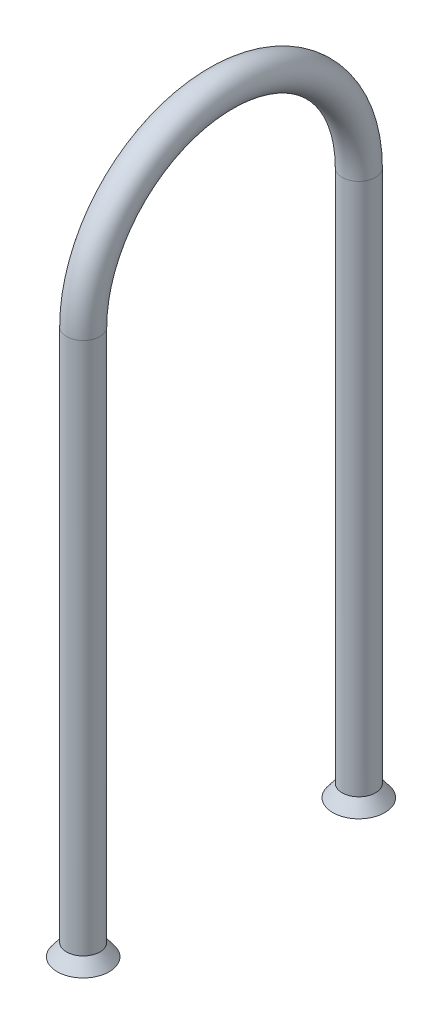
SolidWorks part; units mm, degrees
material "6061-T6 (SS)"
ref_plane "Front Plane" through (0, 0, 0) normal (0, 0, 1) x (1, 0, 0)
ref_plane "Top Plane" through (0, 0, 0) normal (0, 1, 0) x (1, 0, 0)
ref_plane "Right Plane" through (0, 0, 0) normal (1, 0, 0) x (0, 0, -1)
sketch "Sketch8" plane through (0, 0, 0) normal (0, 0, 1) x (1, 0, 0)
  circle A0 centre (0, 0) radius 2.3812
  circle A1 centre (0, 0) radius 1.8224
  dimension "D1" = 0.5588
  dimension "D2" = 4.7625
sketch "Sketch9" plane through (0, 0, 0) normal (1, 0, 0) x (0, 0, -1)
  line L0 (0, 0) -> (0, -19.7022) construction
  line L1 (0, -19.7022) -> (-19.7022, -19.7022) construction
  line L2 (-19.7022, -19.7022) -> (-19.7022, -95.9022)
  arc A0 (0, 0) -> (-19.7022, -19.7022) centre (0, -19.7022) ccw
  dimension "D1" = 19.7022
  dimension "D2" = 76.2
sweep "Sweep2" add profiles "Sketch8" path "Sketch9"
sketch "Sketch10" plane through (0, -95.9022, 0) normal (0, -1, 0) x (1, 0, 0)
  circle A1 centre (0, 19.7022) radius 2.3812 construction
  circle A2 centre (0, 19.7022) radius 2.3812
extrude "Boss-Extrude3" add sketch "Sketch10" along normal blind 1.778 draft 37 draft outward yes
sketch "Sketch11" plane through (0, -95.9022, 0) normal (0, 1, 0) x (1, 0, 0)
  circle A1 centre (0, -19.7022) radius 1.8225
  circle A2 centre (0, -19.7022) radius 1.8224 construction
extrude "Cut-Extrude2" cut sketch "Sketch11" against normal through all draft 37 draft outward yes
mirror "Mirror1" about plane through (0, 0, 0) normal (0, 0, 1) of "Cut-Extrude2", "Boss-Extrude3", "Sweep2"
